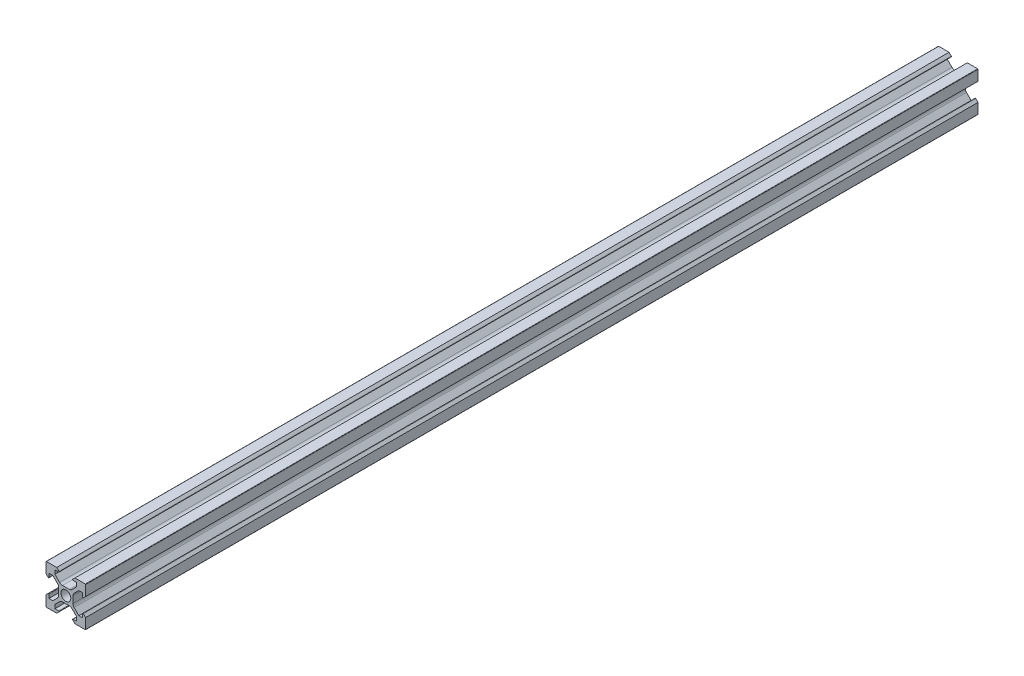
SolidWorks part; units mm, degrees
material "Liga 1350"
ref_plane "Plano frontal" through (0, 0, 0) normal (0, 0, 1) x (1, 0, 0)
ref_plane "Plano superior" through (0, 0, 0) normal (0, 1, 0) x (1, 0, 0)
ref_plane "Plano direito" through (0, 0, 0) normal (1, 0, 0) x (0, 0, -1)
sketch "Esboço1" plane through (0, 0, 0) normal (0, 0, 1) x (1, 0, 0)
  line L0 (0, 13.8681) -> (0, -15.879) construction
  line L1 (-4.6, -10) -> (-9.8, -10)
  line L2 (-3.4414, -8.8414) -> (-4.6, -10)
  line L3 (-4.1858, -3.1251) -> (-6.5607, -5.5)
  line L4 (-10, 9.8) -> (-10, 4.6)
  line L5 (-5.5, -8.5) -> (-3.5828, -8.5)
  line L6 (-5.5, -8.5) -> (-5.5, -6.5607)
  line L7 (-8.5, -5.5) -> (-8.5, -3.5828)
  line L8 (-21.5514, 0) -> (2.5, 0) construction
  line L9 (-3.1251, 4.1858) -> (-5.5, 6.5607)
  line L10 (-8.8414, -3.4414) -> (-10, -4.6)
  line L11 (-8.5, 5.5) -> (-6.5607, 5.5)
  line L12 (-8.8414, 3.4414) -> (-10, 4.6)
  line L13 (-8.5, -5.5) -> (-6.5607, -5.5)
  line L14 (-8.5, 5.5) -> (-8.5, 3.5828)
  line L15 (-3.1251, -4.1858) -> (-5.5, -6.5607)
  line L16 (-21.5514, 0) -> (20.6623, 0) construction
  line L17 (-8.5, 10) -> (-8.5, -10) construction
  line L18 (-10, -9.8) -> (-10, -4.6)
  line L19 (-21.5514, 5.5) -> (20.6623, 5.5) construction
  line L21 (-10, 10) -> (-10, -10) construction
  line L22 (3.6, 1.7109) -> (3.6, 0) construction
  line L23 (21.5514, 0) -> (-2.5, 0) construction
  line L24 (4.6, 10) -> (9.8, 10)
  line L25 (-5.5, 8.5) -> (-5.5, 6.5607)
  line L26 (3.4414, 8.8414) -> (4.6, 10)
  line L27 (-5.5, 8.5) -> (-3.5828, 8.5)
  line L28 (4.1858, 3.1251) -> (6.5607, 5.5)
  line L29 (5.5, 8.5) -> (3.5828, 8.5)
  line L30 (5.5, 8.5) -> (5.5, 6.5607)
  line L31 (-3.6, 1.7109) -> (-3.6, -1.7109)
  line L33 (10, -9.8) -> (10, -4.6)
  line L34 (-4.1858, 3.1251) -> (-6.5607, 5.5)
  line L35 (-3.4414, 8.8414) -> (-4.6, 10)
  line L36 (-4.6, 10) -> (-9.8, 10)
  line L37 (3.1251, -4.1858) -> (5.5, -6.5607)
  line L38 (8.5, 5.5) -> (8.5, 3.5828)
  line L39 (8.5, -5.5) -> (6.5607, -5.5)
  line L40 (8.8414, 3.4414) -> (10, 4.6)
  line L41 (8.5, 5.5) -> (6.5607, 5.5)
  line L42 (8.8414, -3.4414) -> (10, -4.6)
  line L43 (3.1251, 4.1858) -> (5.5, 6.5607)
  line L44 (8.5, -5.5) -> (8.5, -3.5828)
  line L45 (5.5, -8.5) -> (5.5, -6.5607)
  line L46 (5.5, -8.5) -> (3.5828, -8.5)
  line L47 (10, 9.8) -> (10, 4.6)
  line L48 (4.1858, -3.1251) -> (6.5607, -5.5)
  line L49 (3.4414, -8.8414) -> (4.6, -10)
  line L50 (4.6, -10) -> (9.8, -10)
  line L51 (-1.7109, 3.6) -> (1.7109, 3.6)
  line L52 (3.6, 1.7109) -> (3.6, -1.7109)
  line L53 (1.7109, -3.6) -> (-1.7109, -3.6)
  circle A0 centre (0, 0) radius 2.5
  arc A1 (-3.6, 1.7109) -> (-4.1858, 3.1251) centre (-5.6, 1.7109) ccw
  arc A2 (-8.5, 3.5828) -> (-8.8414, 3.4414) centre (-8.7, 3.5828) cw
  arc A3 (-9.8, 10) -> (-10, 9.8) centre (-9.8, 9.8) ccw
  arc A4 (-1.7109, 3.6) -> (-3.1251, 4.1858) centre (-1.7109, 5.6) cw
  arc A5 (-3.5828, 8.5) -> (-3.4414, 8.8414) centre (-3.5828, 8.7) ccw
  arc A6 (-3.5828, -8.5) -> (-3.4414, -8.8414) centre (-3.5828, -8.7) cw
  arc A7 (-1.7109, -3.6) -> (-3.1251, -4.1858) centre (-1.7109, -5.6) ccw
  arc A8 (-9.8, -10) -> (-10, -9.8) centre (-9.8, -9.8) cw
  arc A9 (-8.5, -3.5828) -> (-8.8414, -3.4414) centre (-8.7, -3.5828) ccw
  arc A10 (-3.6, -1.7109) -> (-4.1858, -3.1251) centre (-5.6, -1.7109) cw
  arc A11 (3.6, -1.7109) -> (4.1858, -3.1251) centre (5.6, -1.7109) ccw
  arc A12 (8.5, -3.5828) -> (8.8414, -3.4414) centre (8.7, -3.5828) cw
  arc A13 (9.8, -10) -> (10, -9.8) centre (9.8, -9.8) ccw
  arc A14 (1.7109, -3.6) -> (3.1251, -4.1858) centre (1.7109, -5.6) cw
  arc A15 (3.5828, -8.5) -> (3.4414, -8.8414) centre (3.5828, -8.7) ccw
  arc A16 (3.5828, 8.5) -> (3.4414, 8.8414) centre (3.5828, 8.7) cw
  arc A17 (1.7109, 3.6) -> (3.1251, 4.1858) centre (1.7109, 5.6) ccw
  arc A18 (9.8, 10) -> (10, 9.8) centre (9.8, 9.8) cw
  arc A19 (8.5, 3.5828) -> (8.8414, 3.4414) centre (8.7, 3.5828) ccw
  arc A20 (3.6, 1.7109) -> (4.1858, 3.1251) centre (5.6, 1.7109) cw
  point P0 (0, 0)
  point P45 (-3.6, 2.5393)
extrude "Ressalto-extrusão1" add sketch "Esboço1" along normal blind 450
